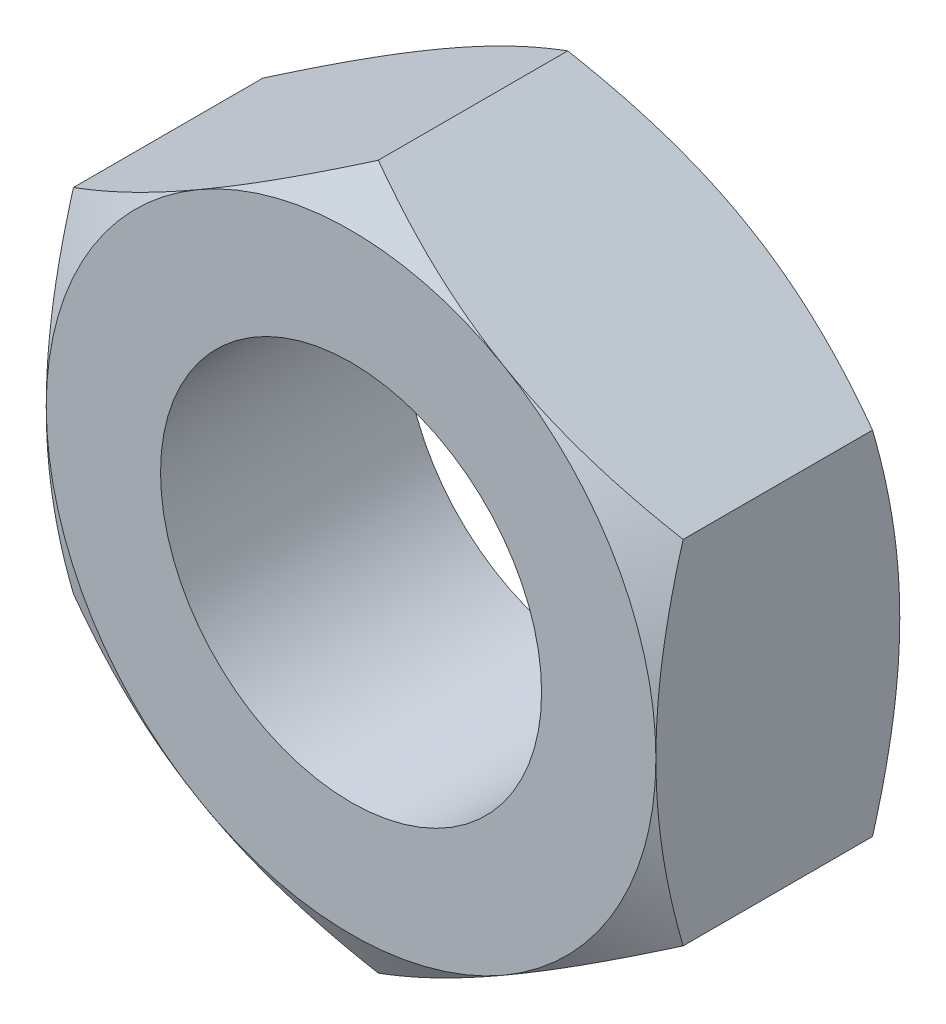
SolidWorks part; units mm, degrees
ref_plane "Front" through (0, 0, 0) normal (0, 0, 1) x (1, 0, 0)
ref_plane "Top" through (0, 0, 0) normal (0, 1, 0) x (1, 0, 0)
ref_plane "Right" through (0, 0, 0) normal (1, 0, 0) x (0, 0, -1)
sketch "Sketch1" plane through (0, 0, 0) normal (0, 0, 1) x (1, 0, 0)
  line L1 (0, 4.6188) -> (-4, 2.3094)
  line L2 (-4, 2.3094) -> (-4, -2.3094)
  line L3 (-4, -2.3094) -> (0, -4.6188)
  line L4 (0, -4.6188) -> (4, -2.3094)
  line L5 (4, -2.3094) -> (4, 2.3094)
  line L6 (4, 2.3094) -> (0, 4.6188)
  circle A0 centre (0, 0) radius 4 construction
  dimension "s" = 8
extrude "Extrude1" add sketch "Sketch1" along normal blind 3.2
sketch "Sketch2" plane through (0, 0, 3.2) normal (0, 0, 1) x (1, 0, 0)
  circle A0 centre (0, 0) radius 2.5
  dimension "d" = 5
extrude "Cut-Extrude1" cut sketch "Sketch2" against normal through all
ref_plane "Plane1" through (0, 0, 1.6) normal (0, 0, 1) x (1, 0, 0)
sketch "Sketch3" plane through (0, 0, 0) normal (1, 0, 0) x (0, 0, -1)
  line L0 (-3.2, 5.6188) -> (-2.2654, 5.6188)
  line L1 (-2.2654, 5.6188) -> (-3.2, 4)
  line L2 (-3.2, 4) -> (-3.2, 5.6188)
  line L3 (-3.2, 4.6188) -> (0, 4.6188) construction
  line L4 (-3.83, 4) -> (0, 4) construction
  line L7 (-3.2, 2.3094) -> (-3.2, 4.6188) construction
  dimension "D1" = 30
  dimension "D2" = 1
revolve "Cut-Revolve1" cut sketch "Sketch3" angle 360 about axis through (0, 0, 0) along (0, 0, 1)
mirror "Mirror1" about plane through (0, 0, 1.6) normal (0, 0, 1) of "Cut-Revolve1"
